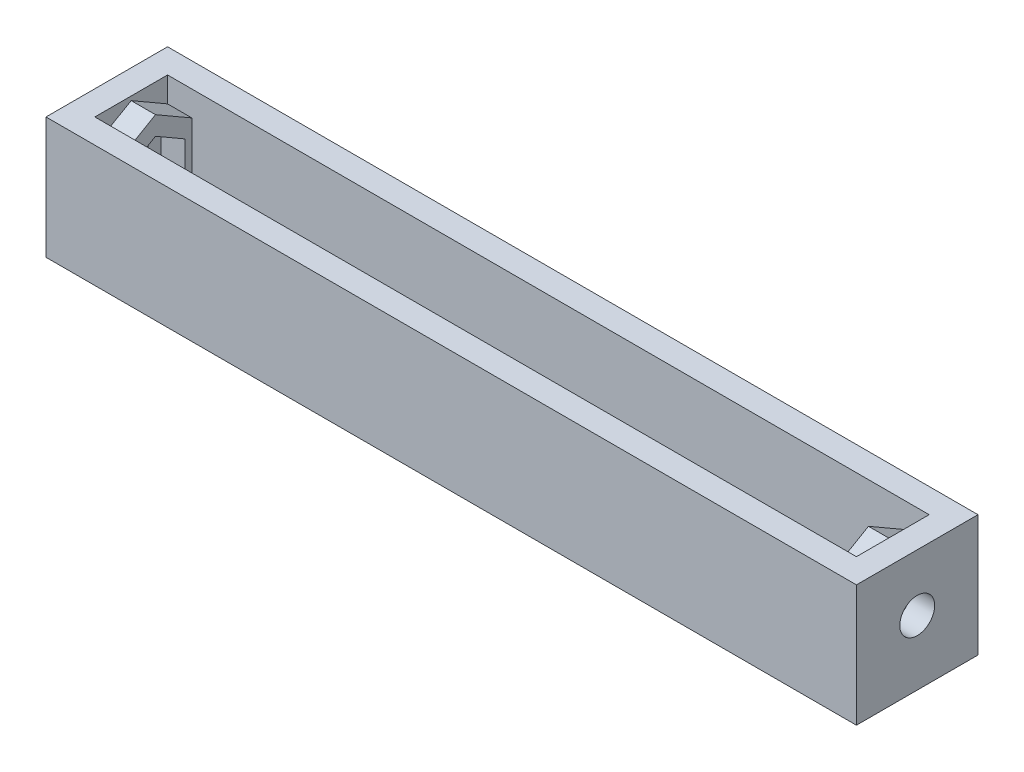
SolidWorks part; units mm, degrees
ref_plane "前视基准面" through (0, 0, 0) normal (0, 0, 1) x (1, 0, 0)
ref_plane "上视基准面" through (0, 0, 0) normal (0, 1, 0) x (1, 0, 0)
ref_plane "右视基准面" through (0, 0, 0) normal (1, 0, 0) x (0, 0, -1)
sketch "草图1" plane through (0, 0, 0) normal (0, 1, 0) x (1, 0, 0)
  line L1 (0, 0) -> (100, 0)
  line L2 (0, 0) -> (0, 15)
  line L3 (0, 15) -> (100, 15)
  line L4 (100, 0) -> (100, 15)
  dimension "D1" = 100
  dimension "D2" = 15
extrude "凸台-拉伸1" add sketch "草图1" along normal blind 15
shell "抽壳1" thickness 3.0127
sketch "草图3" plane through (3.0127, 0, 0) normal (1, 0, 0) x (0, 0, -1)
  line L0 (7.5, 15) -> (7.5, 0) construction
  line L1 (0, 15) -> (15, 15) construction
  line L2 (1.85, 4.7139) -> (7.5, 1.4519)
  line L3 (7.5, 3.7613) -> (11.15, 5.8686)
  line L4 (11.15, 5.8686) -> (11.15, 10.0833)
  line L5 (11.15, 10.0833) -> (7.5, 12.1906)
  line L6 (7.5, 12.1906) -> (3.85, 10.0833)
  line L7 (3.85, 10.0833) -> (3.85, 5.8686)
  line L8 (3.85, 5.8686) -> (7.5, 3.7613)
  line L9 (7.5, 1.4519) -> (13.15, 4.7139)
  line L10 (13.15, 4.7139) -> (13.15, 11.238)
  line L11 (13.15, 11.238) -> (7.5, 14.5)
  line L12 (7.5, 14.5) -> (1.85, 11.238)
  line L13 (1.85, 11.238) -> (1.85, 4.7139)
  line L14 (0, 0) -> (15, 0) construction
  circle A0 centre (7.5, 7.9759) radius 3.65 construction
  point P18 (7.5, 7.2919)
  point P19 (7.5, 0)
  point P22 (7.5, 7.7544)
  dimension "D1" = 7.3
  dimension "D3" = 0.5
  dimension "D2" = 2
extrude "凸台-拉伸2" add sketch "草图3" along normal blind 3
sketch "草图4" plane through (3.0127, 0, 0) normal (1, 0, 0) x (0, 0, -1)
  circle A0 centre (7.5, 7.9759) radius 2.15
  dimension "D1" = 4.3
extrude "切除-拉伸1" cut sketch "草图4" against normal through all
sketch "草图5" plane through (96.9873, 0, 0) normal (-1, 0, 0) x (0, 0, 1)
  line L0 (-7.5, 0) -> (-7.5, 15) construction
  line L2 (-7.5, 12.1906) -> (-11.15, 10.0833)
  line L3 (-11.15, 10.0833) -> (-11.15, 5.8686)
  line L4 (-11.15, 5.8686) -> (-7.5, 3.7613)
  line L5 (-7.5, 3.7613) -> (-3.85, 5.8686)
  line L6 (-3.85, 5.8686) -> (-3.85, 10.0833)
  line L7 (-3.85, 10.0833) -> (-7.5, 12.1906)
  line L8 (-7.5, 14.5) -> (-13.15, 11.238)
  line L9 (-13.15, 11.238) -> (-13.15, 4.7139)
  line L10 (-13.15, 4.7139) -> (-7.5, 1.4519)
  line L11 (-7.5, 1.4519) -> (-1.85, 4.7139)
  line L12 (-1.85, 4.7139) -> (-1.85, 11.238)
  line L13 (-1.85, 11.238) -> (-7.5, 14.5)
  circle A1 centre (-7.5, 7.9759) radius 3.65 construction
  circle A2 centre (-7.5, 7.9759) radius 5.65 construction
  line M1 (-11.9873, 3.0127) -> (-3.0127, 3.0127)
  line M2 (-3.0127, 3.0127) -> (-3.0127, 15)
  line M4 (-11.9873, 15) -> (-11.9873, 3.0127)
extrude "凸台-拉伸3" add sketch "草图5" along normal blind 3 contours L13 L8 L10 L11 L7 L6 L5 L4 L3 L2 M2 M4 M1
sketch "草图6" plane through (96.9873, 0, 0) normal (-1, 0, 0) x (0, 0, 1)
  circle A0 centre (-7.5, 7.9759) radius 2.15
extrude "切除-拉伸2" cut sketch "草图6" against normal through all
